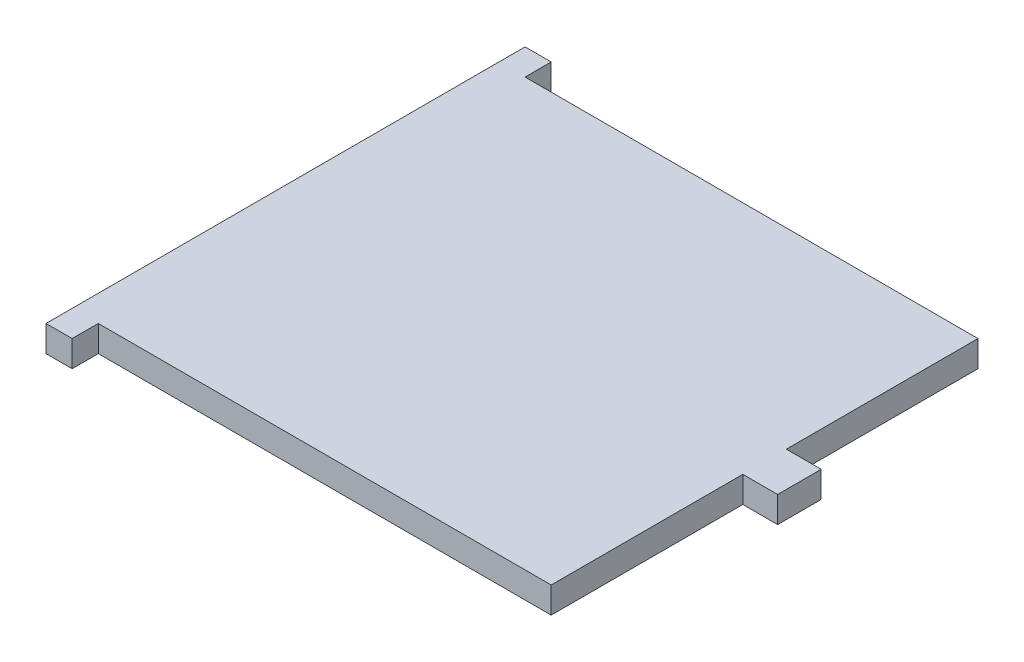
SolidWorks part; units mm, degrees
ref_plane "Front Plane" through (0, 0, 0) normal (0, 0, 1) x (1, 0, 0)
ref_plane "Top Plane" through (0, 0, 0) normal (0, 1, 0) x (1, 0, 0)
ref_plane "Right Plane" through (0, 0, 0) normal (1, 0, 0) x (0, 0, -1)
sketch "Sketch1" plane through (0, 0, 0) normal (0, 1, 0) x (1, 0, 0)
  line L0 (-27.5, -24.5) -> (-27.5, -27.5)
  line L1 (-24.5, -24.5) -> (24.5, -24.5)
  line L2 (-24.5, -24.5) -> (-24.5, 24.5)
  line L3 (-24.5, 24.5) -> (24.5, 24.5)
  line L4 (24.5, -24.5) -> (24.5, 24.5)
  line L5 (-24.5, -24.5) -> (24.5, 24.5) construction
  line L6 (-24.5, 24.5) -> (24.5, -24.5) construction
  line L11 (24.5, 2.5) -> (28.5, 2.5)
  line L12 (24.5, 2.5) -> (24.5, -2.5)
  line L13 (24.5, -2.5) -> (28.5, -2.5)
  line L14 (28.5, 2.5) -> (28.5, -2.5)
  line L15 (-24.5, 24.5) -> (-27.5, 24.5)
  line L16 (-24.5, 24.5) -> (-24.5, -24.5)
  line L17 (-24.5, -24.5) -> (-27.5, -24.5)
  line L18 (-27.5, 24.5) -> (-27.5, -24.5)
  line L23 (-27.5, -27.5) -> (-30.5, -27.5)
  line L24 (-30.5, -27.5) -> (-30.5, 27.5)
  line L25 (-30.5, 27.5) -> (-27.5, 27.5)
  line L26 (-27.5, 27.5) -> (-27.5, 24.5)
  line L27 (28.5, -2.5) -> (24.5, 2.5) construction
  line L28 (28.5, 2.5) -> (24.5, -2.5) construction
  point P0 (0, 0)
  point P8 (26.5, 0)
  point P17 (0, 0)
  dimension "D1" = 49
  dimension "D2" = 3
  dimension "D3" = 3
  dimension "D4" = 3
  dimension "D5" = 5
  dimension "D6" = 4
extrude "Boss-Extrude1" add sketch "Sketch1" along normal blind 3 contours L1 L4 L3 L2 | L14 L11 L4 L13 | L26 L25 L24 L23 L0 L18 | L15 L18 L17 L2
